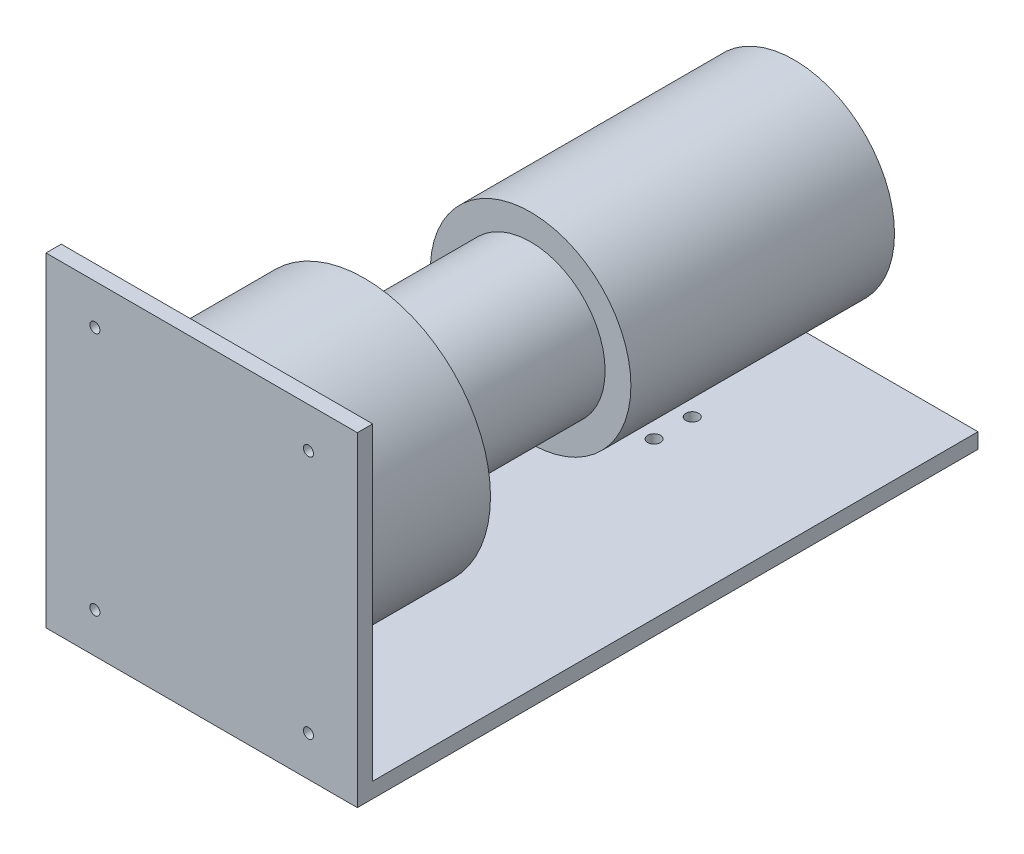
SolidWorks part; units mm, degrees
material "Plomo puro"
ref_plane "Alzado" through (0, 0, 0) normal (0, 0, 1) x (1, 0, 0)
ref_plane "Planta" through (0, 0, 0) normal (0, 1, 0) x (1, 0, 0)
ref_plane "Vista lateral" through (0, 0, 0) normal (1, 0, 0) x (0, 0, -1)
sketch "Croquis1" plane through (0, 0, 0) normal (0, 0, 1) x (1, 0, 0)
  circle A0 centre (0, 0) radius 66
  dimension "D1" = 132
extrude "Saliente-Extruir1" add sketch "Croquis1" along normal blind 80
sketch "Croquis2" plane through (0, 0, 0) normal (0, 0, 1) x (1, 0, 0)
  circle A0 centre (0, 0) radius 39
  dimension "D1" = 78
extrude "Saliente-Extruir2" add sketch "Croquis2" against normal blind 87
ref_plane "Plano1" through (0, 0, -87) normal (0, 0, 1) x (1, 0, 0)
sketch "Croquis4" plane through (0, 0, -87) normal (0, 0, 1) x (1, 0, 0)
  circle A0 centre (0, 0) radius 52.5
  dimension "D1" = 105
extrude "Saliente-Extruir3" add sketch "Croquis4" against normal blind 138
sketch "Croquis5" plane through (0, 0, 0) normal (1, 0, 0) x (0, 0, -1)
  line L0 (-77.1922, 79.3011) -> (-85.1922, 79.3011)
  line L1 (-85.1922, 79.3011) -> (-85.1922, -90.6989)
  line L2 (-85.1922, -90.6989) -> (239.7079, -90.6989)
  line L3 (239.7079, -90.6989) -> (239.7079, -82.6989)
  line L4 (239.7079, -82.6989) -> (-77.1922, -82.6989)
  line L5 (-77.1922, -82.6989) -> (-77.1922, 79.3011)
  dimension "D1" = 8
  dimension "D2" = 8
  dimension "D3" = 170
extrude "Saliente-Extruir4" add sketch "Croquis5" along normal mid plane 163
ref_plane "Plano2" through (0, 0, 85.19) normal (0, 0, 1) x (1, 0, 0)
sketch "Croquis6" plane through (0, 0, 85.19) normal (0, 0, 1) x (1, 0, 0)
  circle A0 centre (-55.9, 58.3011) radius 2.625
  circle A1 centre (55.9, 58.3011) radius 2.625
  circle A2 centre (55.9, -69.6989) radius 2.625
  circle A3 centre (-55.9, -69.6989) radius 2.625
  point P0 (0, 0)
  dimension "D4" = 5.25
  dimension "D5" = 5.25
  dimension "D6" = 5.25
  dimension "D7" = 5.25
extrude "Cortar-Extruir1" cut sketch "Croquis6" against normal mid plane 163
sketch "Sketch1" plane through (0, -82.6989, 0) normal (0, 1, 0) x (1, 0, 0)
  line L0 (0, 225) -> (0, 87) construction
  line L1 (-30, 151.628) -> (30, 151.628) construction
  line L2 (0, 171.628) -> (0, 151.628) construction
  circle A0 centre (0, 151.628) radius 3.35
  circle A1 centre (0, 171.628) radius 3.35
  dimension "D1" = 20
extrude "Cut-Extrude1" cut sketch "Sketch1" along a picked direction on the side against the normal blind 8
